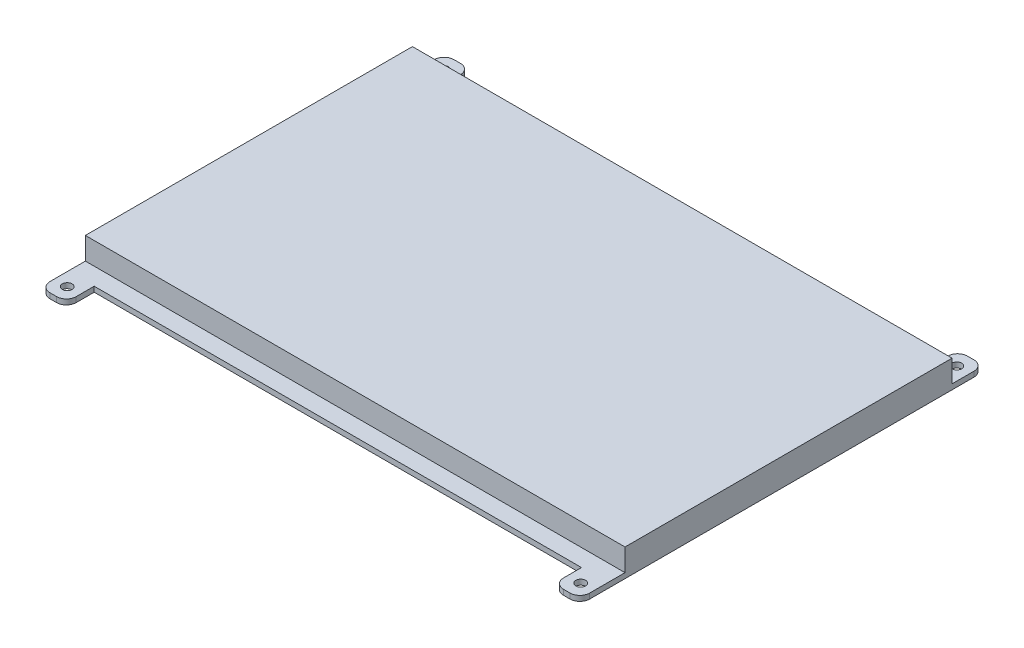
SolidWorks part; units mm, degrees
ref_plane "Alzado" through (0, 0, 0) normal (0, 0, 1) x (1, 0, 0)
ref_plane "Planta" through (0, 0, 0) normal (0, 1, 0) x (1, 0, 0)
ref_plane "Vista lateral" through (0, 0, 0) normal (1, 0, 0) x (0, 0, -1)
sketch "Croquis1" plane through (0, 0, 0) normal (0, 1, 0) x (1, 0, 0)
  line L0 (0, 0) -> (13079.2484, 0) construction
  line L1 (0, 0) -> (0, 13079.2484) construction
  line L2 (82.5, -58.75) -> (82.5, 58.75)
  line L3 (79.5, 61.75) -> (77.5, 61.75)
  line L4 (74.5, 58.75) -> (74.5, 53.25)
  line L5 (74.5, 53.25) -> (-74.5, 53.25)
  line L6 (74.5, -53.25) -> (-74.5, -53.25)
  line L7 (74.5, -58.75) -> (74.5, -53.25)
  line L8 (79.5, -61.75) -> (77.5, -61.75)
  line L9 (-79.5, -61.75) -> (-77.5, -61.75)
  line L10 (-74.5, -58.75) -> (-74.5, -53.25)
  line L11 (-74.5, 58.75) -> (-74.5, 53.25)
  line L12 (-79.5, 61.75) -> (-77.5, 61.75)
  line L13 (-82.5, -58.75) -> (-82.5, 58.75)
  circle A0 centre (78.5, 57.5) radius 1.5
  arc A1 (82.5, 58.75) -> (79.5, 61.75) centre (79.5, 58.75) ccw
  arc A2 (77.5, 61.75) -> (74.5, 58.75) centre (77.5, 58.75) ccw
  arc A3 (77.5, -61.75) -> (74.5, -58.75) centre (77.5, -58.75) cw
  arc A4 (82.5, -58.75) -> (79.5, -61.75) centre (79.5, -58.75) cw
  circle A5 centre (78.5, -57.5) radius 1.5
  circle A6 centre (-78.5, -57.5) radius 1.5
  arc A7 (-82.5, -58.75) -> (-79.5, -61.75) centre (-79.5, -58.75) ccw
  arc A8 (-77.5, -61.75) -> (-74.5, -58.75) centre (-77.5, -58.75) ccw
  arc A9 (-77.5, 61.75) -> (-74.5, 58.75) centre (-77.5, 58.75) cw
  arc A10 (-82.5, 58.75) -> (-79.5, 61.75) centre (-79.5, 58.75) cw
  circle A11 centre (-78.5, 57.5) radius 1.5
  point P17 (78.5, 61.75)
  point P28 (82.5, 0)
  point P44 (-82.5, 0)
  point P46 (0, -53.25)
  point P47 (0, 53.25)
  dimension "D1" = 3
  dimension "D5" = 3
  dimension "D2" = 115
  dimension "D3" = 157
  dimension "D4" = 8
  dimension "D6" = 8.5
  dimension "D7" = 106.5
extrude "Saliente-Extruir1" add sketch "Croquis1" along normal blind 1.6
sketch "Croquis2" plane through (0, 1.6, 0) normal (0, 1, 0) x (1, 0, 0)
  line L0 (-82.5, 58.75) -> (-82.5, -58.75) construction
  line L1 (-82.5, 52.05) -> (82.5, 52.05)
  line L2 (-82.5, 52.05) -> (-82.5, -47.95)
  line L3 (-82.5, -47.95) -> (82.5, -47.95)
  line L4 (82.5, 52.05) -> (82.5, -47.95)
  line L5 (-82.5, 52.05) -> (82.5, -47.95) construction
  line L6 (-82.5, -47.95) -> (82.5, 52.05) construction
  line L7 (82.5, -58.75) -> (82.5, 58.75) construction
  line L8 (74.5, 53.25) -> (-74.5, 53.25) construction
  point P4 (0, 2.05)
  dimension "D1" = 1.2
  dimension "D2" = 100
extrude "Saliente-Extruir2" add sketch "Croquis2" along normal blind 6.8
